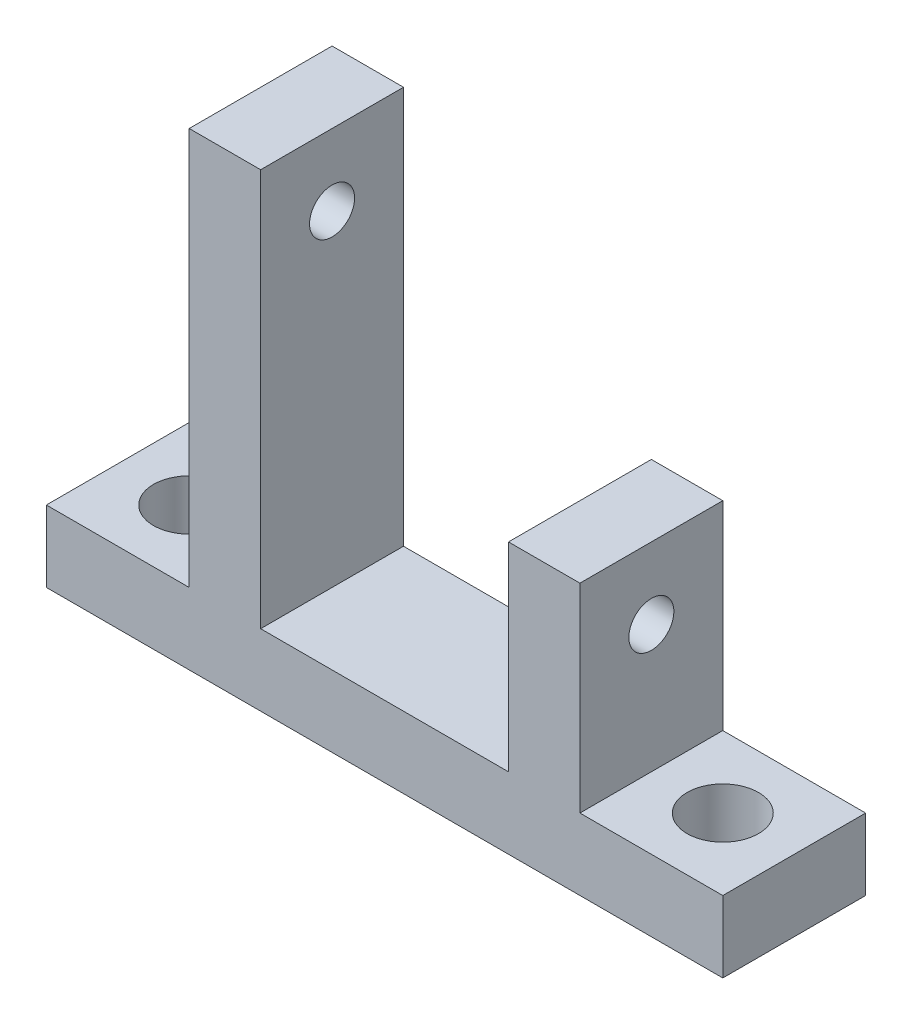
SolidWorks part; units mm, degrees
ref_plane "Front Plane" through (0, 0, 0) normal (0, 0, 1) x (1, 0, 0)
ref_plane "Top Plane" through (0, 0, 0) normal (0, 1, 0) x (1, 0, 0)
ref_plane "Right Plane" through (0, 0, 0) normal (1, 0, 0) x (0, 0, -1)
sketch "Sketch1" plane through (0, 0, 0) normal (0, 0, 1) x (1, 0, 0)
  line L1 (11.0167, 3.175) -> (-11.0167, 3.175)
  line L2 (11.0167, 3.175) -> (11.0167, -3.175)
  line L3 (11.0167, -3.175) -> (-11.0167, -3.175)
  line L4 (-11.0167, 3.175) -> (-11.0167, -3.175)
  line L5 (11.0167, 3.175) -> (-11.0167, -3.175) construction
  line L6 (11.0167, -3.175) -> (-11.0167, 3.175) construction
  line L7 (-11.0167, -3.175) -> (-17.3667, -3.175)
  line L8 (-11.0167, -3.175) -> (-11.0167, 38.5115)
  line L9 (-11.0167, 38.5115) -> (-17.3667, 38.5115)
  line L10 (-17.3667, -3.175) -> (-17.3667, 38.5115)
  line L11 (11.0167, -3.175) -> (17.3667, -3.175)
  line L12 (11.0167, -3.175) -> (11.0167, 20.8737)
  line L13 (11.0167, 20.8737) -> (17.3667, 20.8737)
  line L14 (17.3667, -3.175) -> (17.3667, 20.8737)
  line L15 (17.3667, -3.175) -> (30.0667, -3.175)
  line L16 (17.3667, -3.175) -> (17.3667, 3.175)
  line L17 (17.3667, 3.175) -> (30.0667, 3.175)
  line L18 (30.0667, -3.175) -> (30.0667, 3.175)
  line L19 (-17.3667, -3.175) -> (-30.0667, -3.175)
  line L20 (-17.3667, -3.175) -> (-17.3667, 3.175)
  line L21 (-17.3667, 3.175) -> (-30.0667, 3.175)
  line L22 (-30.0667, -3.175) -> (-30.0667, 3.175)
  point P0 (0, 0)
  point P18 (-11.0167, 31.3978)
  point P19 (-12.477, 25.6639)
  dimension "D1" = 6.35
  dimension "D2" = 6.35
  dimension "D3" = 34.7334
  dimension "D4" = 24.0487
  dimension "D5" = 12.7
  dimension "D6" = 17.6378
extrude "Boss-Extrude1" add sketch "Sketch1" along normal blind 12.7 contours L1 L4 L3 L2 | L10 L7 L4 L8 L9 | L11 L14 L13 L12 L2 | L22 L19 L10 L21 | L15 L18 L17 L14
sketch "Sketch2" plane through (17.3667, 0, 0) normal (1, 0, 0) x (0, 0, -1)
  line L0 (-12.7, 20.8737) -> (0, 20.8737) construction
  line L1 (-12.7, 19.1214) -> (0, 19.1214) construction
  line L2 (-12.7, 3.175) -> (-12.7, 20.8737) construction
  line L3 (0, 3.175) -> (0, 20.8737) construction
  circle A0 centre (-6.35, 14.5237) radius 2
  point P10 (-6.35, 19.1214)
  dimension "D2" = 4
  dimension "D1" = 6.35
extrude "Cut-Extrude1" cut sketch "Sketch2" against normal up to next
sketch "Sketch3" plane through (0, 3.175, 0) normal (0, 1, 0) x (1, 0, 0)
  line L0 (-30.0667, -6.35) -> (-17.3667, -6.35) construction
  line L1 (-30.0667, -12.7) -> (-30.0667, 0) construction
  line L2 (-17.3667, -12.7) -> (-17.3667, 0) construction
  line L3 (17.3667, -6.35) -> (30.0667, -6.35) construction
  line L4 (17.3667, -12.7) -> (17.3667, 0) construction
  line L5 (30.0667, -12.7) -> (30.0667, 0) construction
  circle A0 centre (-23.7167, -6.35) radius 3.175
  circle A1 centre (23.7167, -6.35) radius 3.175
  dimension "D1" = 6.35
extrude "Cut-Extrude2" cut sketch "Sketch3" against normal up to next
sketch "Sketch4" plane through (-17.3667, 0, 0) normal (-1, 0, 0) x (0, 0, 1)
  line L0 (0, 36.4885) -> (12.7, 36.4885) construction
  line L1 (0, 3.175) -> (0, 38.5115) construction
  line L2 (12.7, 3.175) -> (12.7, 38.5115) construction
  line L3 (12.7, 38.5115) -> (0, 38.5115) construction
  circle A0 centre (6.35, 32.1615) radius 2
  point P8 (0, 0)
  point P9 (6.35, 36.4885)
  dimension "D2" = 4
  dimension "D1" = 6.35
extrude "Cut-Extrude3" cut sketch "Sketch4" against normal up to next
